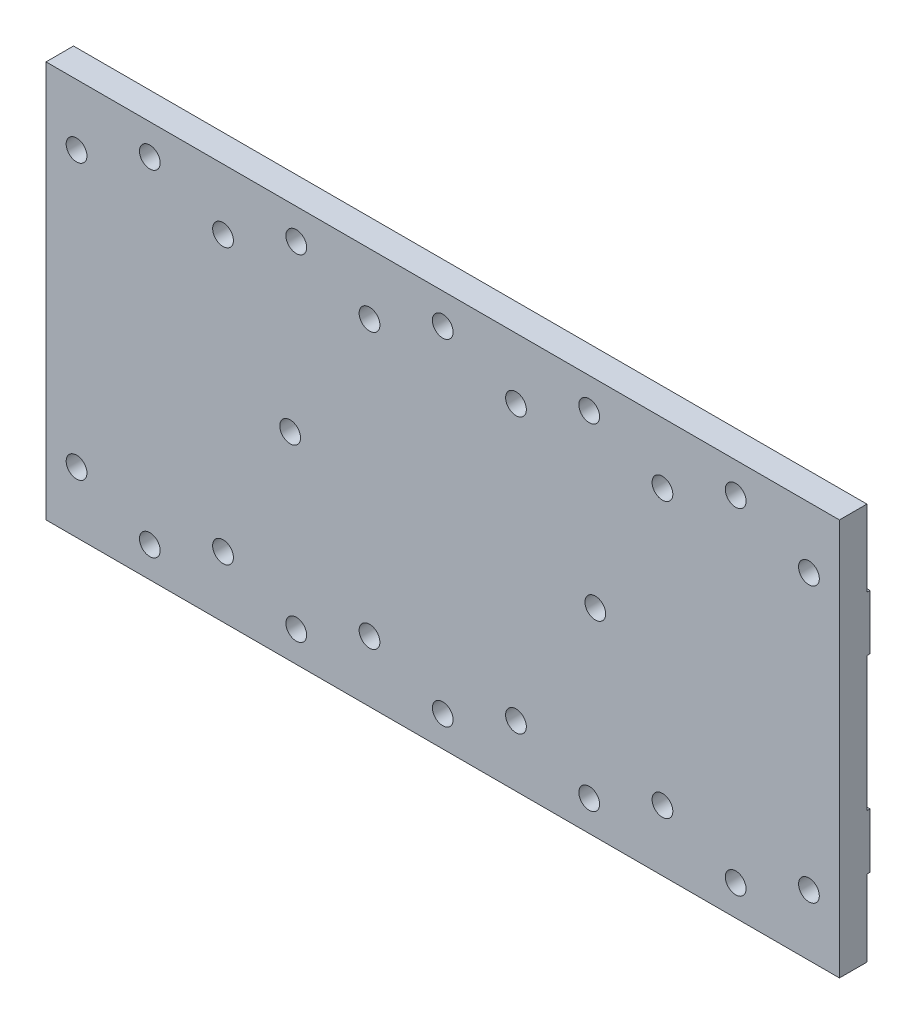
SolidWorks part; units mm, degrees
ref_plane "Plan de face" through (0, 0, 0) normal (0, 0, 1) x (1, 0, 0)
ref_plane "Plan de dessus" through (0, 0, 0) normal (0, 1, 0) x (1, 0, 0)
ref_plane "Plan de droite" through (0, 0, 0) normal (1, 0, 0) x (0, 0, -1)
sketch "Esquisse1" plane through (0, 0, 0) normal (0, 0, 1) x (1, 0, 0)
  line L1 (0, 0) -> (130, 0)
  line L2 (0, 0) -> (0, 65)
  line L3 (0, 65) -> (130, 65)
  line L4 (130, 0) -> (130, 65)
  circle A0 centre (113, 5) radius 1.3
  circle A1 centre (89, 5) radius 1.3
  circle A2 centre (65, 5) radius 1.3
  circle A3 centre (41, 5) radius 1.3
  circle A4 centre (17, 5) radius 1.3
  circle A5 centre (113, 60) radius 1.3
  circle A6 centre (89, 60) radius 1.3
  circle A7 centre (65, 60) radius 1.3
  circle A8 centre (41, 60) radius 1.3
  circle A9 centre (17, 60) radius 1.3
  dimension "D3" = 17
  dimension "D14" = 17
  dimension "D1" = 130
  dimension "D2" = 65
  dimension "D4" = 24
  dimension "D5" = 24
  dimension "D6" = 24
  dimension "D7" = 24
  dimension "D8" = 5
  dimension "D9" = 5
  dimension "D10" = 5
  dimension "D11" = 5
  dimension "D12" = 5
  dimension "D13" = 17
  dimension "D15" = 24
  dimension "D16" = 24
  dimension "D17" = 24
  dimension "D18" = 24
  dimension "D19" = 5
  dimension "D20" = 5
  dimension "D21" = 5
  dimension "D22" = 5
  dimension "D23" = 5
extrude "Boss.-Extru.1" add sketch "Esquisse1" along normal blind 5
sketch "Esquisse2" plane through (0, 0, 0) normal (0, 0, -1) x (-1, 0, 0)
  line L0 (0, 65) -> (0, 0) construction
  line L1 (-130, 65) -> (0, 65)
  line L2 (-130, 65) -> (-130, 52.5)
  line L3 (-130, 52.5) -> (0, 52.5)
  line L4 (0, 65) -> (0, 52.5)
  line L5 (-130, 0) -> (-130, 65) construction
  line L6 (0, 0) -> (-130, 0)
  line L7 (0, 0) -> (0, 12.5)
  line L8 (0, 12.5) -> (-130, 12.5)
  line L9 (-130, 0) -> (-130, 12.5)
  line L11 (-130, 43.5) -> (0, 43.5)
  line L12 (-130, 43.5) -> (-130, 21.5)
  line L13 (-130, 21.5) -> (0, 21.5)
  line L14 (0, 43.5) -> (0, 21.5)
  dimension "D1" = 12.5
  dimension "D2" = 9
  dimension "D3" = 9
  dimension "D4" = 12.5
extrude "Enlèv. mat.-Extru.1" cut sketch "Esquisse2" against normal blind 0.5
hole_wizard "Dégagement M3" positions "Esquisse3" profile "Esquisse4" hole size "M3" standard "ISO"
sketch "Esquisse3" plane through (0, 0, 5) normal (0, 0, 1) x (1, 0, 0)
  point P0 (17, 60)
  point P3 (41, 60)
  point P6 (65, 60)
  point P9 (89, 60)
  point P12 (113, 60)
  point P15 (113, 5)
  point P18 (89, 5)
  point P21 (65, 5)
  point P24 (41, 5)
  point P27 (17, 5)
sketch "Esquisse4" plane through (17, 60, 5) normal (1, 0, 0) x (0, -1, 0)
  line L0 (0, 0) -> (0, 8)
  line L1 (0, 8) -> (1.7, 6.9785)
  line L2 (1.7, 6.9785) -> (1.7, 0)
  line L5 (1.7, 0) -> (0, 0)
  line L10 (0, 8) -> (-1.7, 6.9785) construction
  line L11 (0, -6.35) -> (0, 107.95) construction
  dimension "Diamètre du perçage" = 3.4
  dimension "Profondeur du perçage" = 8
  dimension "Angle de pointe" = 118
sketch "Esquisse5" plane through (0, 0, 0.5) normal (0, 0, -1) x (-1, 0, 0)
  line L0 (0, 0) -> (0, 12.5) construction
  line L1 (0, 52.5) -> (0, 65) construction
  line L2 (0, 65) -> (-130, 65) construction
  line L3 (-130, 0) -> (0, 0) construction
  line L4 (0, 21.5) -> (0, 43.5) construction
  line L5 (-130, 43.5) -> (-130, 21.5) construction
  circle A0 centre (-125, 55) radius 1.3
  circle A1 centre (-101, 55) radius 1.3
  circle A2 centre (-77, 55) radius 1.3
  circle A3 centre (-53, 55) radius 1.3
  circle A4 centre (-29, 55) radius 1.3
  circle A5 centre (-5, 55) radius 1.3
  circle A6 centre (-90, 32.5) radius 1.3
  circle A7 centre (-40, 32.5) radius 1.3
  circle A8 centre (-125, 10) radius 1.3
  circle A9 centre (-101, 10) radius 1.3
  circle A10 centre (-77, 10) radius 1.3
  circle A11 centre (-53, 10) radius 1.3
  circle A12 centre (-29, 10) radius 1.3
  circle A13 centre (-5, 10) radius 1.3
  dimension "D1" = 24
  dimension "D2" = 24
  dimension "D3" = 24
  dimension "D4" = 24
  dimension "D5" = 24
  dimension "D6" = 5
  dimension "D7" = 24
  dimension "D8" = 24
  dimension "D9" = 24
  dimension "D10" = 24
  dimension "D11" = 24
  dimension "D12" = 5
  dimension "D13" = 10
  dimension "D14" = 10
  dimension "D15" = 10
  dimension "D16" = 10
  dimension "D17" = 10
  dimension "D18" = 10
  dimension "D19" = 10
  dimension "D20" = 10
  dimension "D21" = 10
  dimension "D22" = 10
  dimension "D23" = 10
  dimension "D24" = 10
  dimension "D25" = 40
  dimension "D26" = 40
  dimension "D27" = 32.5
  dimension "D28" = 32.5
hole_wizard "Dégagement M32" positions "Esquisse6" profile "Esquisse7" hole size "M3" standard "ISO"
sketch "Esquisse6" plane through (0, 0, 0.5) normal (0, 0, -1) x (-1, 0, 0)
  point P0 (-125, 55)
  point P3 (-101, 55)
  point P6 (-77, 55)
  point P9 (-53, 55)
  point P12 (-29, 55)
  point P15 (-5, 55)
  point P18 (-40, 32.5)
  point P21 (-90, 32.5)
  point P24 (-125, 10)
  point P27 (-101, 10)
  point P30 (-77, 10)
  point P33 (-53, 10)
  point P36 (-29, 10)
  point P39 (-5, 10)
sketch "Esquisse7" plane through (125, 55, 0.5) normal (1, 0, 0) x (0, 1, 0)
  line L0 (0, 0) -> (0, 8)
  line L1 (0, 8) -> (1.7, 6.9785)
  line L2 (1.7, 6.9785) -> (1.7, 0)
  line L5 (1.7, 0) -> (0, 0)
  line L10 (0, 8) -> (-1.7, 6.9785) construction
  line L11 (0, -6.35) -> (0, 107.95) construction
  dimension "Diamètre du perçage" = 3.4
  dimension "Profondeur du perçage" = 8
  dimension "Angle de pointe" = 118
